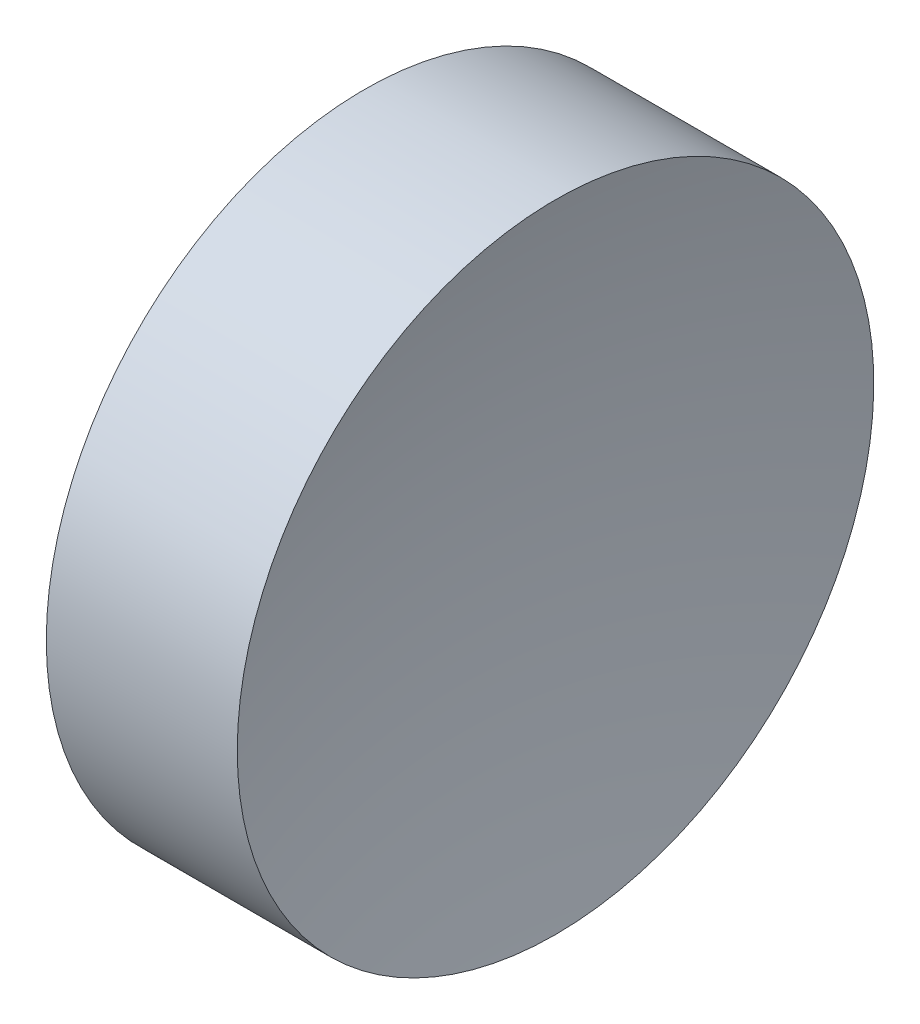
SolidWorks part; units mm, degrees
ref_plane "前视基准面" through (0, 0, 0) normal (0, 0, 1) x (1, 0, 0)
ref_plane "上视基准面" through (0, 0, 0) normal (0, 1, 0) x (1, 0, 0)
ref_plane "右视基准面" through (0, 0, 0) normal (1, 0, 0) x (0, 0, -1)
sketch "草图1" plane through (0, 0, 0) normal (0, 0, 1) x (1, 0, 0)
  line L0 (21.2249, 13.0445) -> (26.692, 13.0445) construction
  line L1 (22.1722, 13.0445) -> (22.1722, 16.1945)
  line L2 (23.6722, 13.0445) -> (22.1722, 13.0445)
  line L3 (22.1722, 16.1945) -> (24.0622, 16.1945)
  arc A0 (24.0622, 16.1945) -> (23.6722, 13.0445) centre (36.5883, 13.0445) ccw
  dimension "D1" = 3.15
revolve "旋转1" add sketch "草图1" angle 360 about L0
